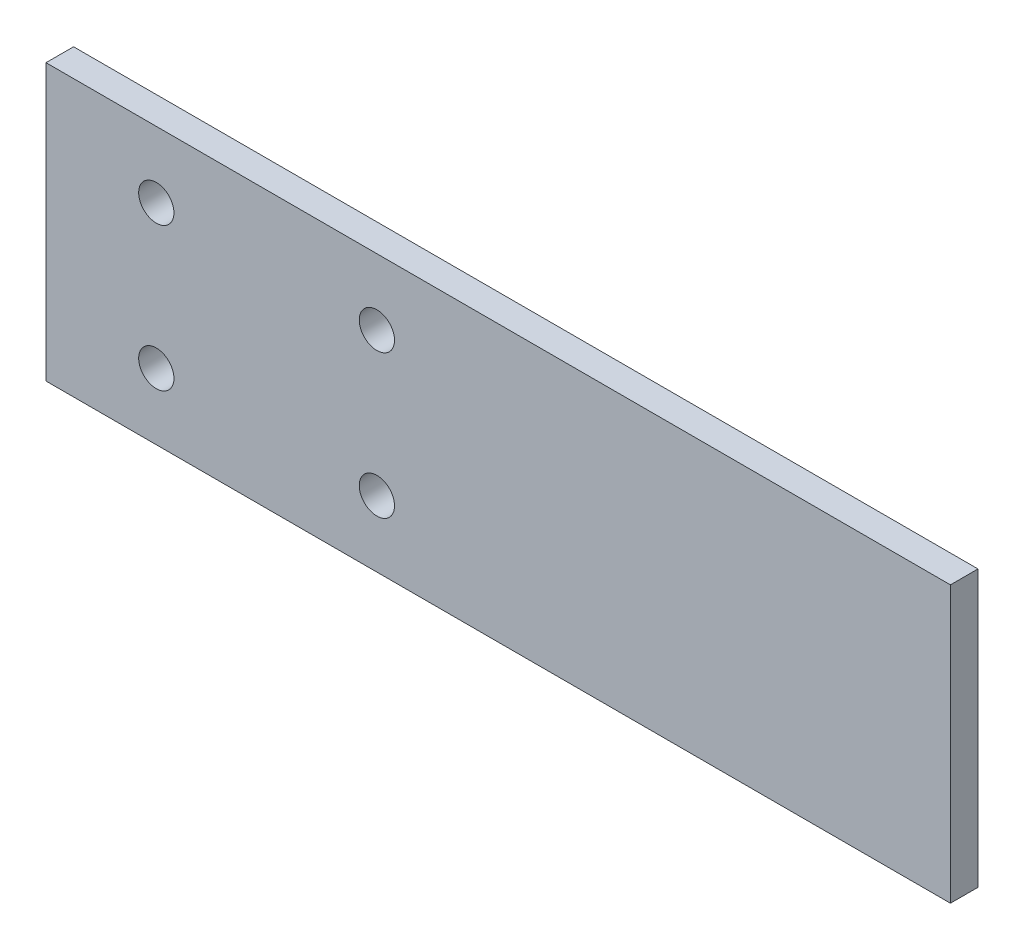
SolidWorks part; units mm, degrees
ref_plane "Front Plane" through (0, 0, 0) normal (0, 0, 1) x (1, 0, 0)
ref_plane "Top Plane" through (0, 0, 0) normal (0, 1, 0) x (1, 0, 0)
ref_plane "Right Plane" through (0, 0, 0) normal (1, 0, 0) x (0, 0, -1)
sketch "Sketch1" plane through (0, 0, 0) normal (0, 0, 1) x (1, 0, 0)
  line L1 (-16.16, 8.92) -> (65.84, 8.92)
  line L2 (-16.16, 8.92) -> (-16.16, -16.08)
  line L3 (-16.16, -16.08) -> (65.84, -16.08)
  line L4 (65.84, 8.92) -> (65.84, -16.08)
  circle A0 centre (-6.16, 2.92) radius 1.6
  circle A1 centre (-6.16, -10.08) radius 1.6
  circle A2 centre (13.84, 2.92) radius 1.6
  circle A3 centre (13.84, -10.08) radius 1.6
  point P12 (0, 0)
  point P13 (0, 0)
  point P14 (0, 0)
  dimension "D2" = 10
  dimension "D1" = 82
  dimension "D4" = 20
  dimension "D5" = 6
  dimension "D6" = 6
extrude "Boss-Extrude1" add sketch "Sketch1" along normal blind 2.5
